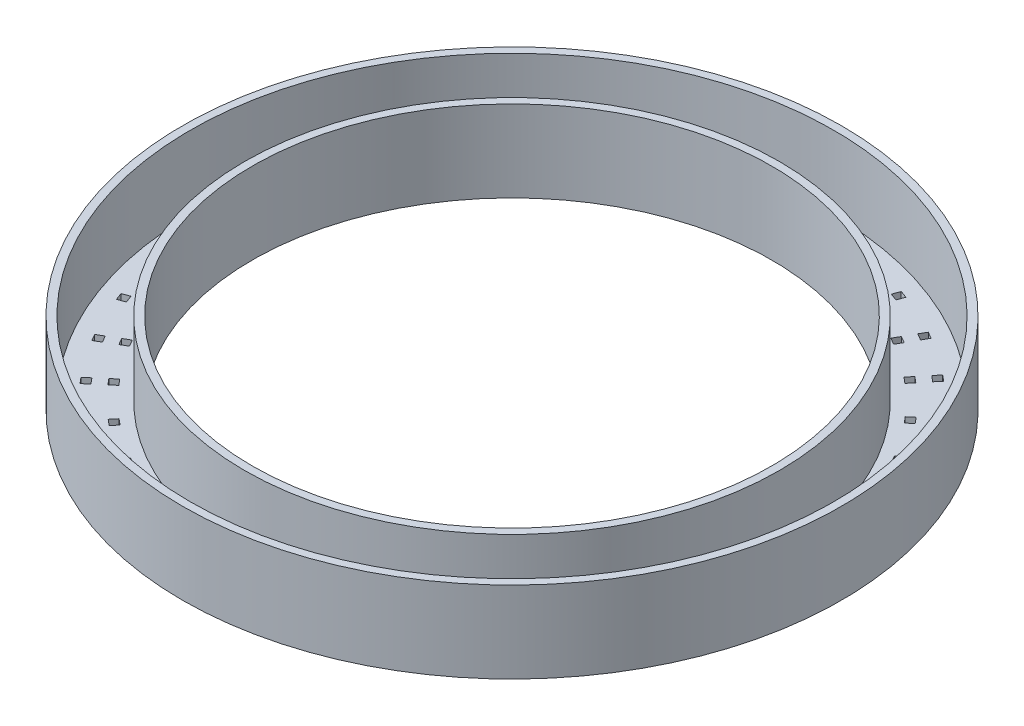
SolidWorks part; units mm, degrees
ref_plane "Front Plane" through (0, 0, 0) normal (0, 0, 1) x (1, 0, 0)
ref_plane "Top Plane" through (0, 0, 0) normal (0, 1, 0) x (1, 0, 0)
ref_plane "Right Plane" through (0, 0, 0) normal (1, 0, 0) x (0, 0, -1)
sketch "Sketch1" plane through (0, 0, 0) normal (0, 1, 0) x (1, 0, 0)
  circle A0 centre (0, 0) radius 42.5
  dimension "D1" = 85
extrude "Boss-Extrude1" add sketch "Sketch1" along normal blind 10.5
sketch "Sketch2" plane through (0, 10.5, 0) normal (0, 1, 0) x (1, 0, 0)
  circle A0 centre (0, 0) radius 33.5
  circle A1 centre (0, 0) radius 42.5 construction
  dimension "D1" = 9
extrude "Cut-Extrude1" cut sketch "Sketch2" against normal through all
shell "Shell1" thickness 1
sketch "Sketch4" plane through (0, 1, 0) normal (0, 1, 0) x (1, 0, 0)
  line L1 (-0.6588, 35.9359) -> (0.3412, 35.9359)
  line L2 (-0.6588, 35.9359) -> (-0.6588, 36.9359)
  line L3 (-0.6588, 36.9359) -> (0.3412, 36.9359)
  line L4 (0.3412, 35.9359) -> (0.3412, 36.9359)
  line L5 (-0.682, 38.4827) -> (0.318, 38.4827)
  line L6 (-0.682, 38.4827) -> (-0.682, 39.4827)
  line L7 (-0.682, 39.4827) -> (0.318, 39.4827)
  line L8 (0.318, 38.4827) -> (0.318, 39.4827)
  circle A2 centre (0, 0) radius 42.5 construction
  point P0 (0, 38)
  dimension "D1" = 38
  dimension "D2" = 1
  dimension "D3" = 1
  dimension "D4" = 1
  dimension "D5" = 1
extrude "Cut-Extrude3" cut sketch "Sketch4" against normal through all
pattern_circular "CirPattern1" count 36 every 10 about axis through (0, 0, 0) along (0, 1, 0) of "Cut-Extrude3"
